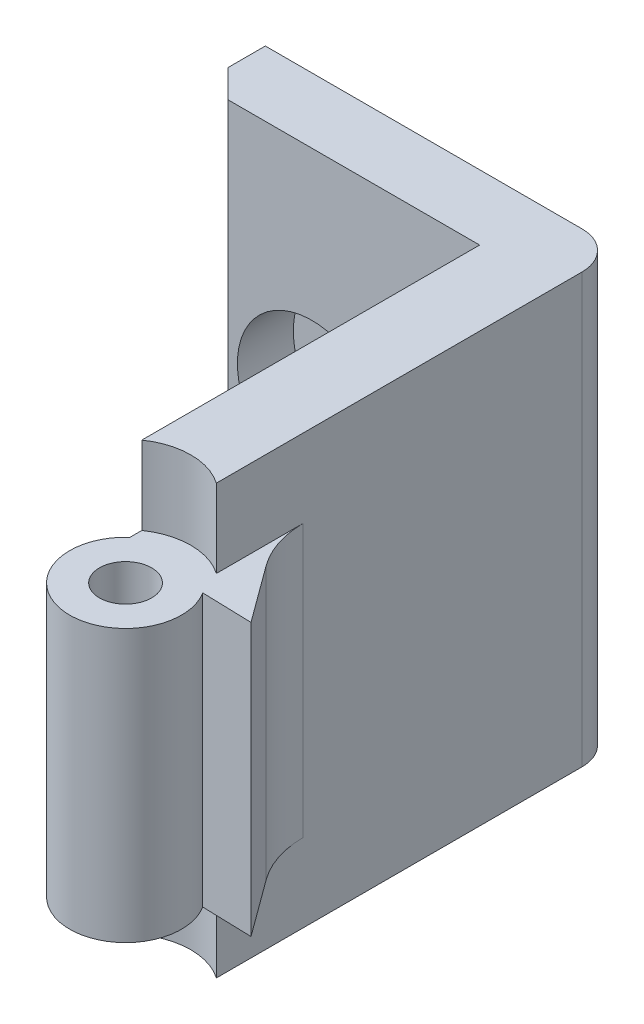
SolidWorks part; units mm, degrees
ref_plane "Front Plane" through (0, 0, 0) normal (0, 0, 1) x (1, 0, 0)
ref_plane "Top Plane" through (0, 0, 0) normal (0, 1, 0) x (1, 0, 0)
ref_plane "Right Plane" through (0, 0, 0) normal (1, 0, 0) x (0, 0, -1)
sketch "Sketch1" plane through (0, 0, 0) normal (0, 1, 0) x (1, 0, 0)
  line L1 (-19.7132, 15.2353) -> (-4.7132, 15.2353)
  line L2 (-19.7132, 15.2353) -> (-19.7132, 11.7353)
  line L3 (-19.7132, 11.7353) -> (-4.7132, 11.7353)
  line L4 (-4.7132, 15.2353) -> (-4.7132, 11.7353)
  line L5 (-4.7132, 15.2353) -> (-0.7132, 15.2353)
  line L6 (-4.7132, 15.2353) -> (-4.7132, -9.2647)
  line L7 (-4.7132, -9.2647) -> (-0.7132, -9.2647)
  line L8 (-0.7132, 15.2353) -> (-0.7132, -9.2647)
  dimension "D1" = 3.5
  dimension "D2" = 19
  dimension "D3" = 24.5
  dimension "D4" = 4
extrude "Boss-Extrude1" add sketch "Sketch1" along normal blind 23 contours L4 L1 L2 L3 | L8 L5 L4 L6 L7
sketch "Sketch3" plane through (0, 0, 0) normal (0, -1, 0) x (1, 0, 0)
  line L0 (-4.7132, 9.2647) -> (-0.7132, 9.2647) construction
  circle A0 centre (-2.7132, 9.2647) radius 3
  dimension "D1" = 6
extrude "Boss-Extrude2" add sketch "Sketch3" against normal up to surface (23 mm away) up to face at (-8.3799, 23, -5.902)
sketch "Sketch4" plane through (0, 0, 0) normal (0, -1, 0) x (1, 0, 0)
  circle A0 centre (-2.7132, 9.2647) radius 1.4
  arc A1 (-0.7132, 7.0286) -> (-4.7132, 7.0286) centre (-2.7132, 9.2647) ccw construction
  dimension "D1" = 2.8
extrude "Cut-Extrude1" cut sketch "Sketch4" against normal blind 23
sketch "Sketch5" plane through (0, 0, 0) normal (0, -1, 0) x (1, 0, 0)
  circle A0 centre (-2.7132, 9.2647) radius 3.5
  circle A1 centre (-2.7132, 9.2647) radius 1.4 construction
  dimension "D1" = 7
extrude "Cut-Extrude2" cut sketch "Sketch5" against normal blind 4.2
sketch "Sketch6" plane through (0, 23, 0) normal (0, 1, 0) x (1, 0, 0)
  circle A0 centre (-2.7132, -9.2647) radius 3.5
  circle A1 centre (-2.7132, -9.2647) radius 1.4 construction
  dimension "D1" = 7
extrude "Cut-Extrude3" cut sketch "Sketch6" against normal blind 4.2
sketch "Sketch7" plane through (0, 0, -11.7353) normal (0, 0, 1) x (1, 0, 0)
  line L0 (-19.7132, 23) -> (-4.7132, 23) construction
  line L1 (-19.7132, 23) -> (-19.7132, 0) construction
  circle A0 centre (-13.7132, 11) radius 4
  dimension "D1" = 12
  dimension "D2" = 6
  dimension "D3" = 8
extrude "Cut-Extrude4" cut sketch "Sketch7" against normal blind 3
chamfer "Chamfer1" distance 1.5 angle 45 1 edges at (-19.7132, 11.5, -11.7353)
sketch "Sketch8" plane through (0, 18.8, 0) normal (0, 1, 0) x (1, 0, 0)
  line L0 (-0.9223, -7.6375) -> (2.4895, -7.7364)
  line L1 (2.4895, -7.7364) -> (-0.9223, -3.081)
  line L2 (-0.9223, -3.081) -> (-0.9223, -7.6375)
  point P2 (4.188, -7.6375)
  point P4 (2.4895, -7.7364)
extrude "Boss-Extrude3" add sketch "Sketch8" against normal up to surface (14.6 mm away) up to face at (-2.7132, 4.2, 7.8647)
fillet "Fillet1" radius 2 1 edges at (-0.7132, 11.5, -15.2353)
fillet "Fillet2" radius 5 1 edges at (-0.7132, 11.5, 3.3664)
